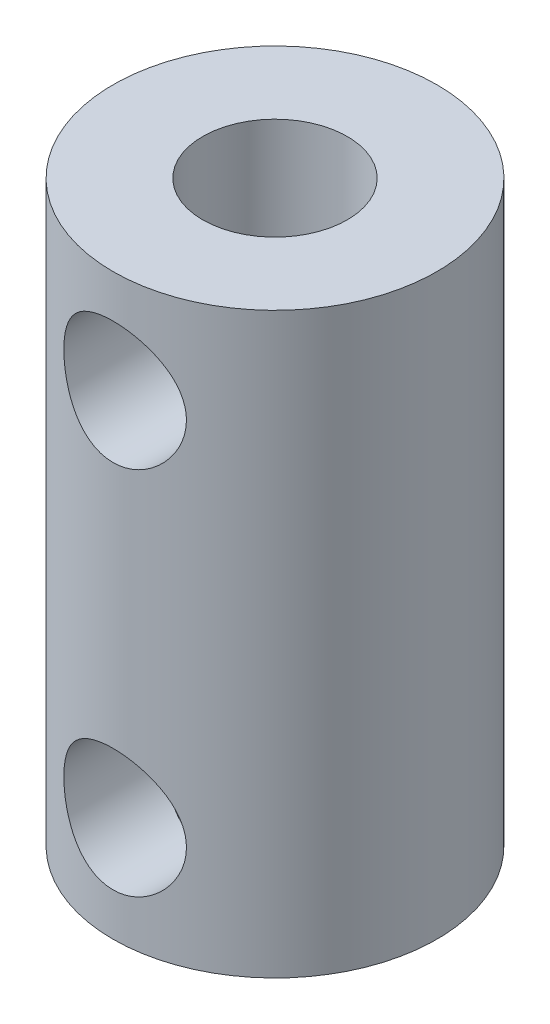
SolidWorks part; units mm, degrees
ref_plane "Front Plane" through (0, 0, 0) normal (0, 0, 1) x (1, 0, 0)
ref_plane "Top Plane" through (0, 0, 0) normal (0, 1, 0) x (1, 0, 0)
ref_plane "Right Plane" through (0, 0, 0) normal (1, 0, 0) x (0, 0, -1)
sketch "Sketch1" plane through (0, 0, 0) normal (0, 1, 0) x (1, 0, 0)
  circle A0 centre (0, 0) radius 5.334
  dimension "D1" = 10.668
extrude "Boss-Extrude1" add sketch "Sketch1" along normal blind 19.05
hole_wizard "3/16 (0.1875) Dowel Hole2" positions "Sketch3" profile "Sketch2" hole size "3/16" standard "ANSI Inch"
sketch "Sketch3" plane through (0, 19.05, 0) normal (0, 1, 0) x (1, 0, 0)
  point P0 (0, 0)
sketch "Sketch2" plane through (0, 19.05, 0) normal (1, 0, 0) x (0, 0, 1)
  line L0 (0, 0) -> (0, 10.9558)
  line L1 (0, 10.9558) -> (2.3812, 9.525)
  line L2 (2.3812, 9.525) -> (2.3812, 0)
  line L5 (2.3812, 0) -> (0, 0)
  line L10 (0, 10.9558) -> (-2.3813, 9.525) construction
  line L11 (0, -6.35) -> (0, 107.95) construction
  dimension "Hole Dia." = 4.7625
  dimension "Hole Depth" = 9.525
  dimension "Drill Angle" = 118
hole_wizard "Ø5.0mm Dowel Hole2" positions "Sketch5" profile "Sketch4" hole size "Ø5.0" standard "ANSI Metric"
sketch "Sketch5" plane through (0, 0, 0) normal (0, -1, 0) x (-1, 0, 0)
  point P0 (0, 0)
sketch "Sketch4" plane through (0, 0, 0) normal (1, 0, 0) x (0, 0, -1)
  line L0 (0, 0) -> (0, 11.0272)
  line L1 (0, 11.0272) -> (2.5, 9.525)
  line L2 (2.5, 9.525) -> (2.5, 0)
  line L5 (2.5, 0) -> (0, 0)
  line L10 (0, 11.0272) -> (-2.5, 9.525) construction
  line L11 (0, -6.35) -> (0, 107.95) construction
  dimension "Hole Dia." = 5
  dimension "Hole Depth" = 9.525
  dimension "Drill Angle" = 118
ref_plane "Plane1" through (0, 0, 9.6817) normal (0, 0, 1) x (1, 0, 0)
hole_wizard "#10-32 Tapped Hole1" positions "Sketch8" profile "Sketch7" tap size "#10-32" standard "ANSI Inch"
sketch "Sketch8" plane through (0, 0, 9.6817) normal (0, 0, 1) x (1, 0, 0)
  line L0 (5.334, 19.05) -> (-5.334, 19.05) construction
  line L1 (-5.334, 0) -> (5.334, 0) construction
  point P0 (0, 15.621)
  point P2 (0, 3.429)
  dimension "D1" = 3.429
  dimension "D2" = 3.429
sketch "Sketch7" plane through (0, 15.621, 9.6817) normal (1, 0, 0) x (0, -1, 0)
  line L0 (0, 0) -> (0, 7.3004)
  line L1 (0, 7.3004) -> (2.0193, 7.3004)
  line L2 (2.0193, 7.3004) -> (2.0193, 0)
  line L5 (2.0193, 0) -> (0, 0)
  line L11 (0, -6.35) -> (0, 107.95) construction
  dimension "Thru Tap Drill Dia." = 4.0386
  dimension "Thru Tap Drill Depth" = 7.3004
cosmetic thread "Hole Thread1"
cosmetic thread "Hole Thread2"
